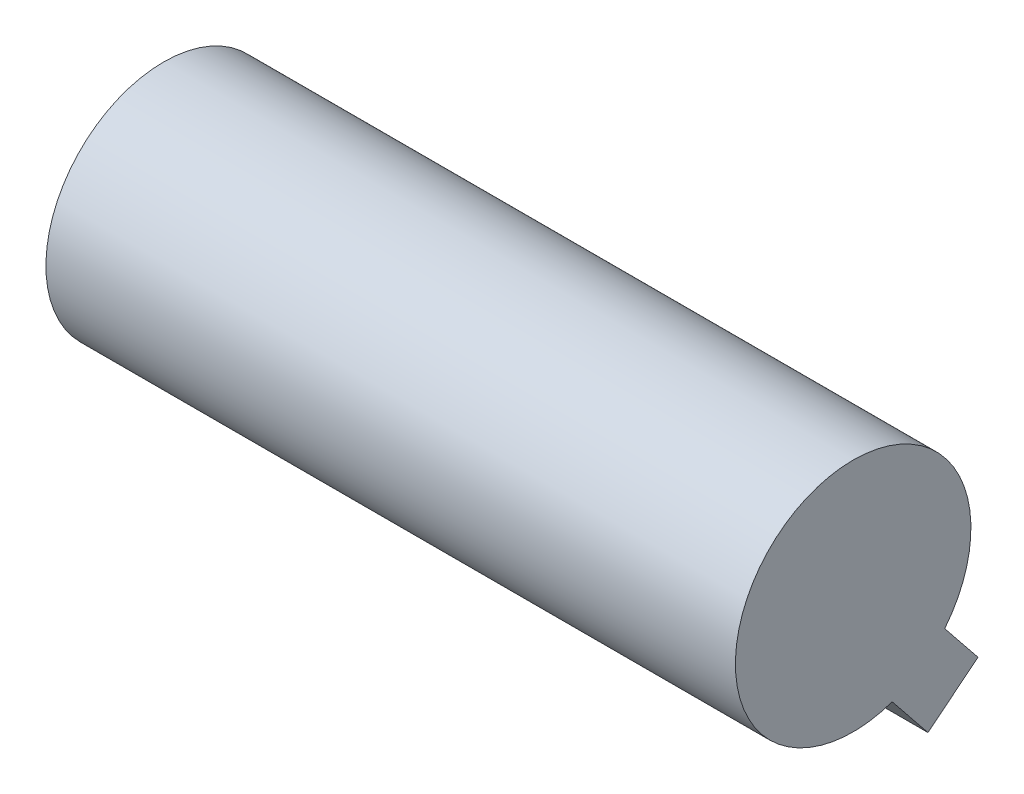
SolidWorks part; units mm, degrees
ref_plane "Front Plane" through (0, 0, 0) normal (0, 0, 1) x (1, 0, 0)
ref_plane "Top Plane" through (0, 0, 0) normal (0, 1, 0) x (1, 0, 0)
ref_plane "Right Plane" through (0, 0, 0) normal (1, 0, 0) x (0, 0, -1)
sketch "Sketch1" plane through (0, 0, 0) normal (1, 0, 0) x (0, 0, -1)
  circle A0 centre (0, 0) radius 7
  dimension "D1" = 14
extrude "Boss-Extrude1" add sketch "Sketch1" along normal blind 40.99
ref_plane "Plane1" through (0, -5.4574, -4.3836) normal (0, -0.7796, -0.6262) x (1, 0, 0)
sketch "Sketch2" plane through (0, -5.4574, -4.3836) normal (0, -0.7796, -0.6262) x (1, 0, 0)
  line L0 (0, 7) -> (0, -7) construction
  line L1 (0, 2.3296) -> (14.3372, 2.3296)
  line L2 (0, 2.3296) -> (0, -1.4859)
  line L3 (0, -1.4859) -> (14.3372, -1.4859)
  line L4 (14.3372, 2.3296) -> (14.3372, -1.4859)
  line L5 (40.99, -7) -> (40.99, 7) construction
  line L6 (40.99, 2.3296) -> (26.3736, 2.3296)
  line L7 (40.99, 2.3296) -> (40.99, -1.4859)
  line L8 (40.99, -1.4859) -> (26.3736, -1.4859)
  line L9 (26.3736, 2.3296) -> (26.3736, -1.4859)
extrude "Boss-Extrude2" add sketch "Sketch2" along normal blind 3 separate body
sketch "Sketch3" plane through (0, -5.4574, -4.3836) normal (0, 0.7796, 0.6262) x (1, 0, 0)
  line L1 (40.99, -2.3296) -> (26.3736, -2.3296)
  line L2 (40.99, -2.3296) -> (40.99, 1.4859)
  line L3 (40.99, 1.4859) -> (26.3736, 1.4859)
  line L4 (26.3736, -2.3296) -> (26.3736, 1.4859)
  line L5 (14.3372, 1.4859) -> (0, 1.4859)
  line L6 (14.3372, 1.4859) -> (14.3372, -2.3296)
  line L7 (14.3372, -2.3296) -> (0, -2.3296)
  line L8 (0, 1.4859) -> (0, -2.3296)
extrude "Boss-Extrude3" add sketch "Sketch3" along normal blind 10
